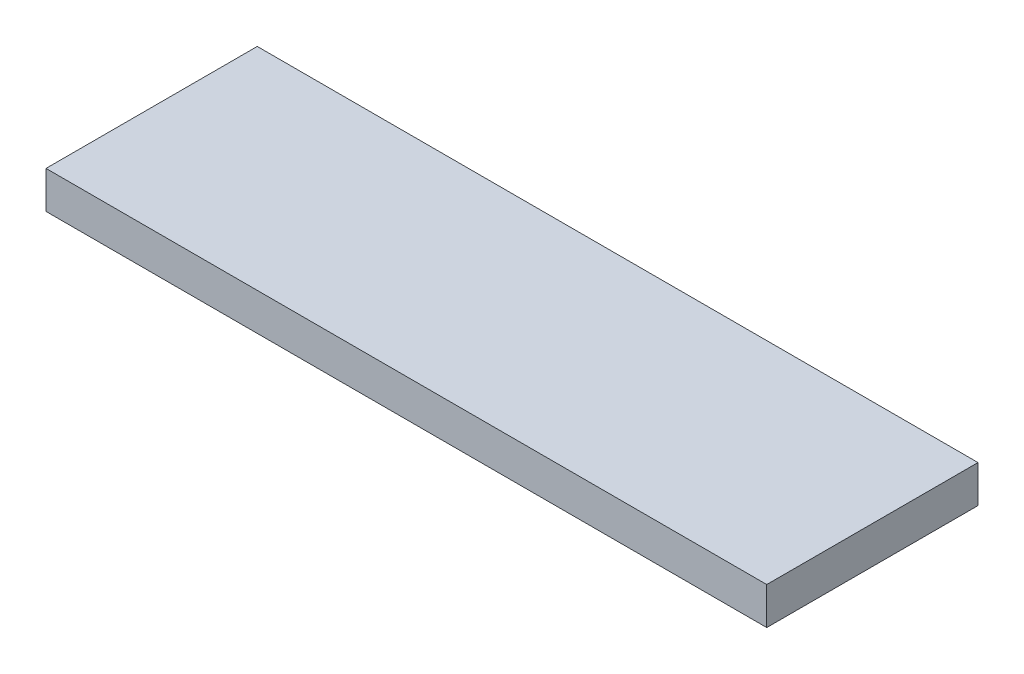
SolidWorks part; units mm, degrees
ref_plane "Спереди" through (0, 0, 0) normal (0, 0, 1) x (1, 0, 0)
ref_plane "Сверху" through (0, 0, 0) normal (0, 1, 0) x (1, 0, 0)
ref_plane "Справа" through (0, 0, 0) normal (1, 0, 0) x (0, 0, -1)
sketch "Эскиз1" plane through (0, 0, 0) normal (1, 0, 0) x (0, 0, -1)
  line L0 (0, 0) -> (0, 300)
  line L1 (0, 300) -> (1700, 300)
  line L2 (1700, 300) -> (1700, 0)
  line L7 (1700, 0) -> (0, 0)
extrude "Бобышка-Вытянуть1" add sketch "Эскиз1" along normal blind 5800
sketch "Эскиз2" plane through (0, 0, 0) normal (0, -1, 0) x (1, 0, 0)
  line L0 (1750, -250) -> (1750, -1450)
  line L1 (400, -250) -> (1400, -250)
  line L2 (400, -250) -> (400, -1450)
  line L3 (400, -1450) -> (1400, -1450)
  line L4 (1400, -250) -> (1400, -1450)
  line L5 (1750, -250) -> (2750, -250)
  line L6 (1750, -1450) -> (2750, -1450)
  line L7 (2750, -250) -> (2750, -1450)
  line L8 (3100, -250) -> (3100, -1450)
  line L9 (3100, -250) -> (4100, -250)
  line L10 (3100, -1450) -> (4100, -1450)
  line L11 (4100, -250) -> (4100, -1450)
  line L12 (4450, -250) -> (4450, -1450)
  line L13 (4450, -250) -> (5450, -250)
  line L14 (4450, -1450) -> (5450, -1450)
  line L15 (5450, -250) -> (5450, -1450)
  dimension "D1" = 4
extrude "Вырез-Вытянуть1" cut sketch "Эскиз2" against normal blind 100
fillet "Скругление1" radius 40 1 edges at (400, 100, -850)
